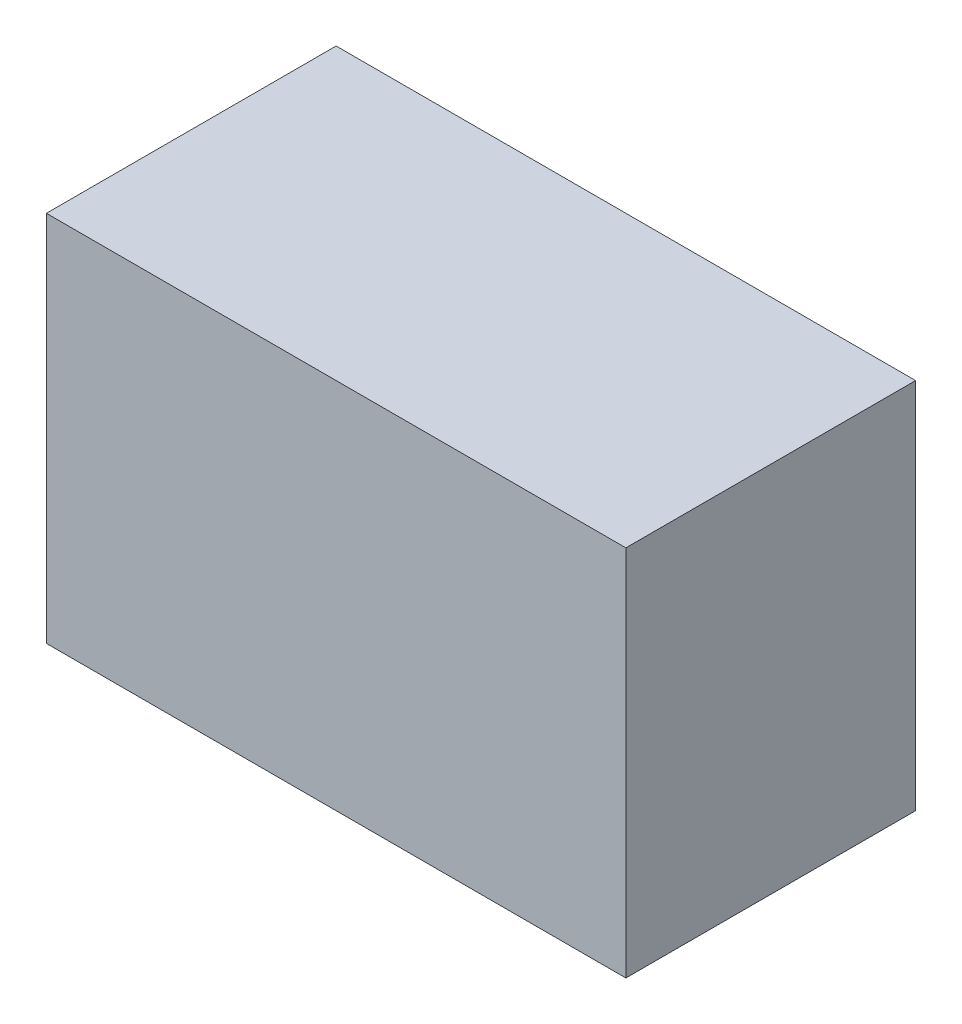
SolidWorks part; units mm, degrees
material "Pine"
ref_plane "Front Plane" through (0, 0, 0) normal (0, 0, 1) x (1, 0, 0)
ref_plane "Top Plane" through (0, 0, 0) normal (0, 1, 0) x (1, 0, 0)
ref_plane "Right Plane" through (0, 0, 0) normal (1, 0, 0) x (0, 0, -1)
sketch "Sketch1" plane through (0, 0, 0) normal (0, 1, 0) x (1, 0, 0)
  line L0 (0, -55) -> (0, 55) construction
  line L1 (-700, 350) -> (700, 350)
  line L2 (-700, 350) -> (-700, -350)
  line L3 (-700, -350) -> (700, -350)
  line L4 (700, 350) -> (700, -350)
  line L5 (-55, 0) -> (55, 0) construction
  dimension "D1" = 1400
  dimension "D2" = 700
  dimension "D3" = 700
  dimension "D4" = 350
extrude "Boss-Extrude1" add sketch "Sketch1" against normal blind 900
